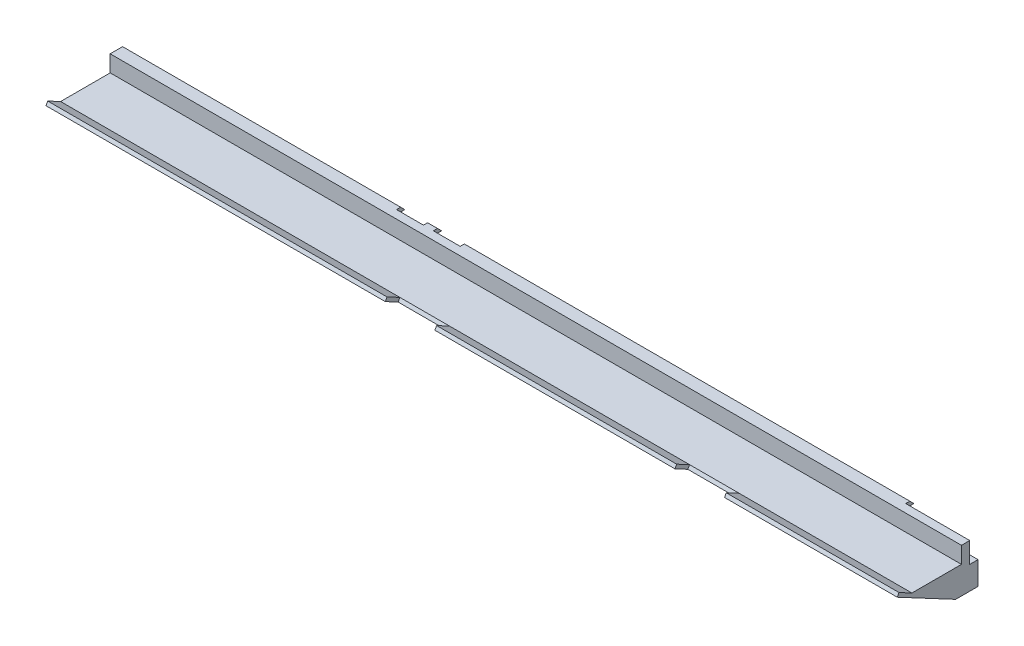
SolidWorks part; units mm, degrees
ref_plane "Front Plane" through (0, 0, 0) normal (0, 0, 1) x (1, 0, 0)
ref_plane "Top Plane" through (0, 0, 0) normal (0, 1, 0) x (1, 0, 0)
ref_plane "Right Plane" through (0, 0, 0) normal (1, 0, 0) x (0, 0, -1)
sketch "Sketch1" plane through (0, 0, 0) normal (1, 0, 0) x (0, 0, -1)
  line L0 (0, 0) -> (16, 0) construction
  line L2 (0, 1) -> (12, 1)
  line L10 (0, 1) -> (-3.1173, 2.6575)
  line L11 (0, 0) -> (-3.5318, 1.8779)
  line L13 (12, 1) -> (12, 4)
  line L15 (14, 4) -> (14, 2)
  line L16 (14, 2) -> (16, 2)
  line L17 (16, 2) -> (16, -5.6337)
  line L18 (16, -5.6337) -> (10.5954, -5.6337)
  line L19 (10.5954, -5.6337) -> (0, 0)
  line L20 (0, 1) -> (0, 8.2097) construction
  line L21 (-3.5318, 1.8779) -> (-3.1173, 2.6575)
  line L22 (14, 4) -> (16, 4)
  line L24 (15, 5) -> (12, 5)
  line L25 (12, 5) -> (12, 4)
  line L26 (16, 4) -> (15, 5)
  dimension "D1" = 12
  dimension "D2" = 1
  dimension "D3" = 14
  dimension "D5" = 4
  dimension "D6" = 28
  dimension "D7" = 2
  dimension "D8" = 2
  dimension "D9" = 2
  dimension "D10" = 2
extrude "Extrude profile" add sketch "Sketch1" along normal blind 206
sketch "Sketch6" plane through (0, 0, -16) normal (0, 0, -1) x (-1, 0, 0)
  line L0 (-206, 1) -> (0, 1) construction
  line L1 (-206, 1) -> (0, 1) construction
  line L2 (-206, -5.6337) -> (0, -5.6337) construction
  line L3 (-200, -5.6337) -> (-15, -5.6337)
  line L4 (-200, -5.6337) -> (-200, 0)
  line L5 (-200, 0) -> (-15, 0)
  line L6 (-15, -5.6337) -> (-15, 0)
  line L7 (-206, -5.6337) -> (-206, 2) construction
  line L8 (0, -5.6337) -> (0, 2) construction
  dimension "D1" = 6
  dimension "D2" = 1
  dimension "D3" = 15
extrude "Air space" cut sketch "Sketch6" against normal blind 45
sketch "Sketch7" plane through (0, 0.7796, -0.4145) normal (0, 0.8829, -0.4695) x (1, 0, 0)
  line L0 (206, -4) -> (0, -4) construction
  line L1 (164.2, -4) -> (152.2, -4)
  line L2 (164.2, -4) -> (164.2, -0.4695)
  line L3 (164.2, -0.4695) -> (152.2, -0.4695)
  line L4 (152.2, -4) -> (152.2, -0.4695)
  line L5 (206, -0.4695) -> (0, -0.4695) construction
  line L6 (206, -0.4695) -> (206, -4) construction
  line L7 (94.1, -4) -> (82.1, -4)
  line L8 (94.1, -4) -> (94.1, -0.4695)
  line L9 (94.1, -0.4695) -> (82.1, -0.4695)
  line L10 (82.1, -4) -> (82.1, -0.4695)
  point P14 (206, -2.2347)
  dimension "D1" = 41.8
  dimension "D2" = 111.9
  dimension "D3" = 12
extrude "Tab cuts" cut sketch "Sketch7" against normal through all
sketch "Sketch8" plane through (0, 0, -16) normal (0, 0, -1) x (-1, 0, 0)
  line L0 (-15, 0) -> (-200, 0) construction
  line L1 (-206, 0) -> (-190.5, 0)
  line L2 (-206, 0) -> (-206, 10)
  line L3 (-206, 10) -> (-190.5, 10)
  line L4 (-190.5, 0) -> (-190.5, 10)
  line L5 (-206, -5.6337) -> (-206, 2) construction
  line L7 (-73.8, 0) -> (-67.3, 0)
  line L8 (-73.8, 0) -> (-73.8, 10)
  line L9 (-73.8, 10) -> (-67.3, 10)
  line L10 (-67.3, 0) -> (-67.3, 10)
  line L11 (-82.7, 0) -> (-76.2, 0)
  line L12 (-82.7, 0) -> (-82.7, 10)
  line L13 (-82.7, 10) -> (-76.2, 10)
  line L14 (-76.2, 0) -> (-76.2, 10)
  dimension "D1" = 15.5
  dimension "D2" = 10
  dimension "D3" = 6.5
  dimension "D4" = 123.3
  dimension "D5" = 132.2
extrude "Cut-Extrude1" cut sketch "Sketch8" against normal blind 2
